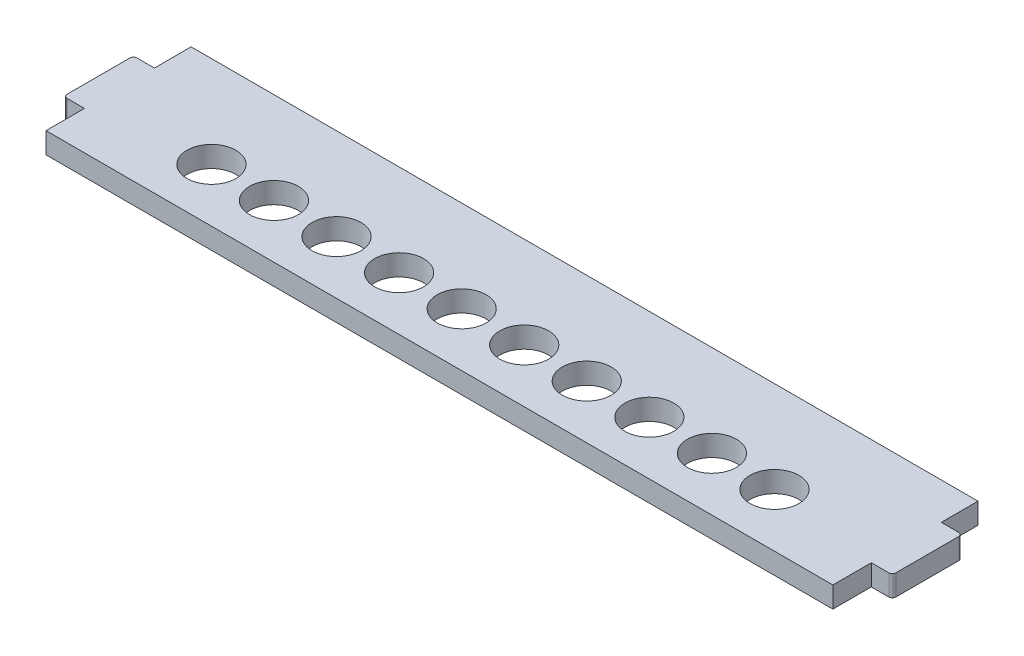
SolidWorks part; units mm, degrees
ref_plane "Спереди" through (0, 0, 0) normal (0, 0, 1) x (1, 0, 0)
ref_plane "Сверху" through (0, 0, 0) normal (0, 1, 0) x (1, 0, 0)
ref_plane "Справа" through (0, 0, 0) normal (1, 0, 0) x (0, 0, -1)
sketch "Эскиз1" plane through (0, 0, 0) normal (0, 1, 0) x (1, 0, 0)
  line L0 (0, -20.75) -> (0, 21.8864) construction
  line L1 (-56.25, -20.75) -> (56.25, -20.75)
  line L2 (56.25, -20.75) -> (56.25, -15.25)
  line L5 (56.25, -15.25) -> (59.25, -15.25)
  line L6 (59.25, -15.25) -> (59.25, -5.25)
  line L7 (59.25, -5.25) -> (56.25, -5.25)
  line L8 (56.25, -5.25) -> (56.25, 0)
  line L9 (56.25, 0) -> (-56.25, 0)
  line L10 (-56.25, -5.25) -> (-56.25, 0)
  line L11 (-59.25, -5.25) -> (-56.25, -5.25)
  line L12 (-59.25, -15.25) -> (-59.25, -5.25)
  line L13 (-56.25, -15.25) -> (-59.25, -15.25)
  line L16 (-56.25, -20.75) -> (-56.25, -15.25)
  line L17 (-50, -9.6) -> (-50, -8.3845) construction
  line L18 (-40.25, -13.1) -> (-40.25, -9.6) construction
  line L19 (-40.25, -9.6) -> (-50, -9.6) construction
  line L22 (50, -9.6) -> (50, -8.2086) construction
  circle A0 centre (-40.25, -13.1) radius 3.5
  circle A1 centre (-31.3056, -13.1) radius 3.5
  circle A2 centre (-22.3611, -13.1) radius 3.5
  circle A3 centre (-13.4167, -13.1) radius 3.5
  circle A4 centre (-4.4722, -13.1) radius 3.5
  circle A5 centre (4.4722, -13.1) radius 3.5
  circle A6 centre (13.4167, -13.1) radius 3.5
  circle A7 centre (22.3611, -13.1) radius 3.5
  circle A8 centre (31.3056, -13.1) radius 3.5
  circle A9 centre (40.25, -13.1) radius 3.5
  circle A11 centre (49.1944, -13.1) radius 3.5 [skipped]
  point P14 (50, -9.6)
  point P18 (0, 0)
  point P25 (-50, -9.6)
  dimension "D5" = 7
  dimension "D11" = 6.25
  dimension "D1" = 3
  dimension "D2" = 10
  dimension "D3" = 6.25
  dimension "D4" = 20.75
  dimension "D6" = 5.25
  dimension "D7" = 100
  dimension "D8" = 6.25
  dimension "D9" = 9.6
  dimension "D12" = 3.5
  dimension "D10" = 11
extrude "Бобышка-Вытянуть1" add sketch "Эскиз1" along normal blind 3
fillet "Скругление1" radius 0.5 4 edges at (-59.25, 1.5, 5.25) (-59.25, 1.5, 15.25) (59.25, 1.5, 5.25) (59.25, 1.5, 15.25)
